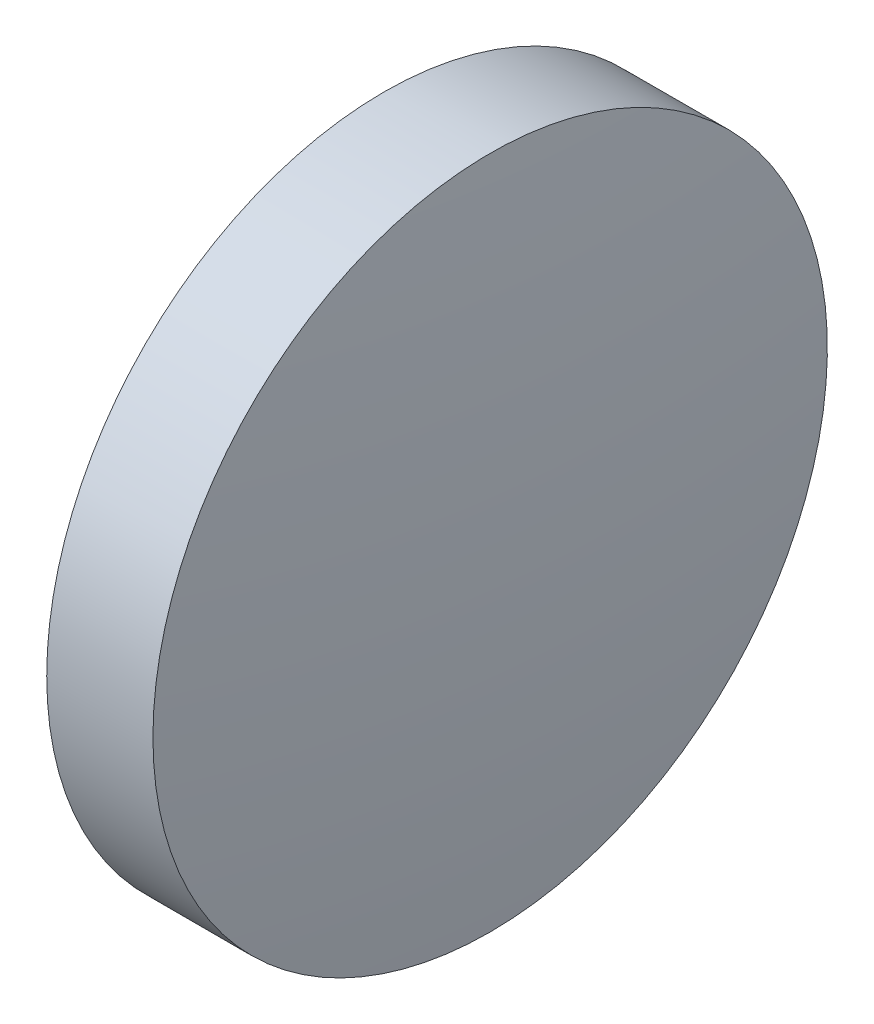
SolidWorks part; units mm, degrees
ref_plane "前视基准面" through (0, 0, 0) normal (0, 0, 1) x (1, 0, 0)
ref_plane "上视基准面" through (0, 0, 0) normal (0, 1, 0) x (1, 0, 0)
ref_plane "右视基准面" through (0, 0, 0) normal (1, 0, 0) x (0, 0, -1)
sketch "草图1" plane through (0, 0, 0) normal (0, 0, 1) x (1, 0, 0)
  line L0 (39.6527, 24.3081) -> (46.7386, 24.3081) construction
  line L1 (42.2291, 30.6581) -> (44.2291, 30.6581)
  line L2 (44.2291, 30.6581) -> (44.2291, 17.9581)
  line L3 (44.2291, 17.9581) -> (42.2291, 17.9581)
  line L4 (42.2291, 17.9581) -> (42.2291, 30.6581)
  arc A0 (42.2291, 30.6581) -> (42.2291, 17.9581) centre (99.6916, 24.3081) ccw
  arc A1 (44.2291, 17.9581) -> (44.2291, 30.6581) centre (-13.2334, 24.3081) ccw
  dimension "D1" = 12.7
  dimension "D2" = 2.0001
revolve "旋转1" add sketch "草图1" angle 360 about L0
